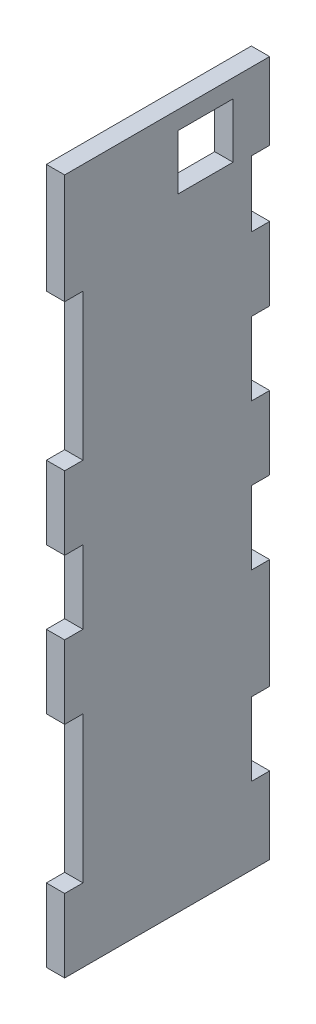
SolidWorks part; units mm, degrees
ref_plane "Front Plane" through (0, 0, 0) normal (0, 0, 1) x (1, 0, 0)
ref_plane "Top Plane" through (0, 0, 0) normal (0, 1, 0) x (1, 0, 0)
ref_plane "Right Plane" through (0, 0, 0) normal (1, 0, 0) x (0, 0, -1)
sketch "Sketch1" plane through (0, 0, 0) normal (0, 0, 1) x (1, 0, 0)
  line L0 (-158.75, -241.3) -> (-133.35, -241.3) construction
  line L1 (-139.7, -241.3) -> (-133.35, -241.3)
  line L2 (-139.7, -241.3) -> (-139.7, 0)
  line L3 (-139.7, 0) -> (-133.35, 0)
  line L4 (-133.35, -241.3) -> (-133.35, 0)
  dimension "D1" = 6.35
extrude "Boss-Extrude1" add sketch "Sketch1" against normal blind 71.12
sketch "Sketch2" plane through (-133.35, 0, 0) normal (1, 0, 0) x (0, 0, -1)
  line L0 (64.77, -246.38) -> (64.77, -214.63) construction
  line L1 (71.12, -241.3) -> (64.77, -241.3)
  line L3 (71.12, -214.63) -> (64.77, -214.63)
  line L5 (71.12, -241.3) -> (71.12, 0) construction
  line L6 (71.12, -189.23) -> (64.77, -189.23)
  line L8 (71.12, -151.13) -> (64.77, -151.13)
  line L10 (64.77, -189.23) -> (64.77, -151.13) construction
  line L11 (64.77, -125.73) -> (64.77, -100.33) construction
  line L12 (71.12, -125.73) -> (64.77, -125.73)
  line L14 (71.12, -100.33) -> (64.77, -100.33)
  line L16 (64.77, -74.93) -> (64.77, -49.53) construction
  line L17 (71.12, -74.93) -> (64.77, -74.93)
  line L19 (71.12, -49.53) -> (64.77, -49.53)
  line L21 (64.77, -26.67) -> (64.77, 5.08) construction
  line L22 (71.12, -26.67) -> (64.77, -26.67)
  line L24 (71.12, 0) -> (64.77, 0)
  line L27 (71.12, -151.13) -> (64.77, -151.13) construction
  line L28 (64.77, -49.53) -> (71.12, -49.53) construction
  line L29 (71.12, -74.93) -> (64.77, -74.93)
  line L30 (64.77, -26.67) -> (71.12, -26.67)
  line L31 (64.77, -26.67) -> (64.77, -49.53)
  line L32 (64.77, -49.53) -> (71.12, -49.53)
  line L33 (71.12, -26.67) -> (71.12, -49.53)
  line L34 (71.12, -74.93) -> (71.12, -100.33)
  line L35 (71.12, -100.33) -> (64.77, -100.33)
  line L36 (64.77, -74.93) -> (64.77, -100.33)
  line L37 (64.77, -125.73) -> (71.12, -125.73)
  line L38 (64.77, -125.73) -> (64.77, -151.13)
  line L39 (64.77, -151.13) -> (71.12, -151.13)
  line L40 (71.12, -125.73) -> (71.12, -151.13)
  line L41 (64.77, -189.23) -> (71.12, -189.23)
  line L42 (64.77, -189.23) -> (64.77, -214.63)
  line L43 (64.77, -214.63) -> (71.12, -214.63)
  line L44 (71.12, -189.23) -> (71.12, -214.63)
  line M14 (71.12, -241.3) -> (71.12, 0)
  dimension "D1" = 26.67
  dimension "D2" = 25.4
  dimension "D3" = 38.1
  dimension "D4" = 25.4
  dimension "D5" = 25.4
  dimension "D6" = 25.4
  dimension "D7" = 25.4
  dimension "D8" = 22.86
  dimension "D9" = 26.67
extrude "Cut-Extrude1" cut sketch "Sketch2" against normal blind 6.35 contours L22 L31 L19 M14 | L17 L36 L14 M14 | L12 L38 L8 M14 | L6 L42 L3 M14
sketch "Sketch3" plane through (-133.35, 0, 0) normal (1, 0, 0) x (0, 0, -1)
  line L0 (0, -241.3) -> (0, 0) construction
  line L1 (0, -215.9) -> (6.35, -215.9)
  line L2 (0, -215.9) -> (0, -165.1)
  line L3 (0, -165.1) -> (6.35, -165.1)
  line L4 (6.35, -215.9) -> (6.35, -165.1)
  line L5 (71.12, -241.3) -> (0, -241.3) construction
  line L6 (0, -139.7) -> (6.35, -139.7)
  line L7 (0, -139.7) -> (0, -114.3)
  line L8 (0, -114.3) -> (6.35, -114.3)
  line L9 (6.35, -139.7) -> (6.35, -114.3)
  line L10 (0, -88.9) -> (6.35, -88.9)
  line L11 (0, -88.9) -> (0, -38.1)
  line L12 (0, -38.1) -> (6.35, -38.1)
  line L13 (6.35, -88.9) -> (6.35, -38.1)
  dimension "D1" = 25.4
  dimension "D2" = 50.8
  dimension "D3" = 25.4
  dimension "D4" = 25.4
  dimension "D5" = 25.4
  dimension "D6" = 50.8
  dimension "D7" = 6.35
extrude "Cut-Extrude2" cut sketch "Sketch3" against normal blind 6.35
sketch "Sketch4" plane through (-139.7, 0, 0) normal (-1, 0, 0) x (0, 0, 1)
  line L0 (-64.77, -26.67) -> (-64.77, 0) construction
  line L1 (-39.37, -6.35) -> (-58.42, -6.35)
  line L2 (-39.37, -6.35) -> (-39.37, -25.4)
  line L3 (-39.37, -25.4) -> (-58.42, -25.4)
  line L4 (-58.42, -6.35) -> (-58.42, -25.4)
  line L5 (-71.12, 0) -> (0, 0) construction
  dimension "D1" = 6.35
  dimension "D2" = 6.35
  dimension "D3" = 19.05
  dimension "D4" = 19.05
extrude "Cut-Extrude3" cut sketch "Sketch4" against normal through all
